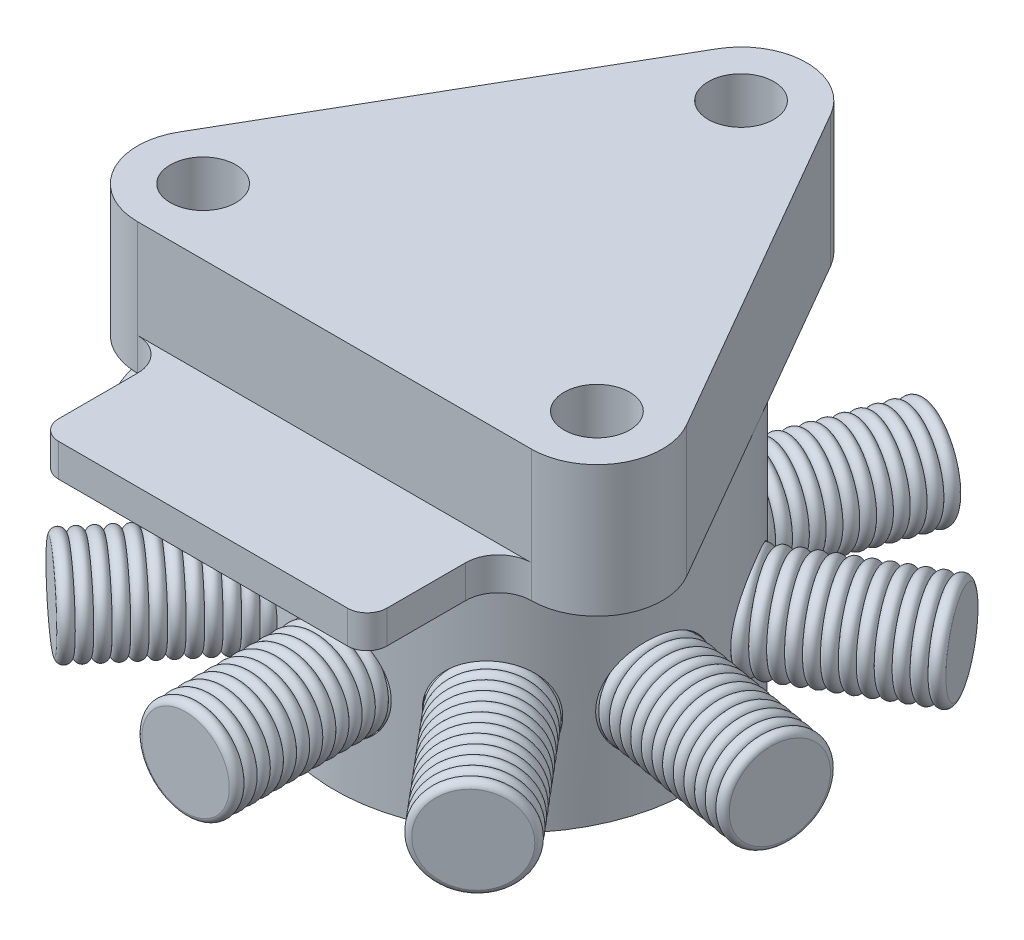
SolidWorks part; units mm, degrees
ref_plane "Plano frontal" through (0, 0, 0) normal (0, 0, 1) x (1, 0, 0)
ref_plane "Plano superior" through (0, 0, 0) normal (0, 1, 0) x (1, 0, 0)
ref_plane "Plano direito" through (0, 0, 0) normal (1, 0, 0) x (0, 0, -1)
sketch "Esboço1" plane through (0, 0, 0) normal (0, 1, 0) x (1, 0, 0)
  line L0 (0.866, 3.9641) -> (3.866, -1.2321)
  line L1 (3, -2.7321) -> (-3, -2.7321)
  line L2 (-3.866, -1.2321) -> (-0.866, 3.9641)
  circle A0 centre (0, 3.4641) radius 0.5
  circle A1 centre (3, -1.7321) radius 0.5
  circle A2 centre (-3, -1.7321) radius 0.5
  arc A3 (0.866, 3.9641) -> (-0.866, 3.9641) centre (0, 3.4641) ccw
  arc A4 (-3.866, -1.2321) -> (-3, -2.7321) centre (-3, -1.7321) ccw
  arc A5 (3, -2.7321) -> (3.866, -1.2321) centre (3, -1.7321) ccw
  circle A6 centre (0, 3.4641) radius 1 construction
  circle A7 centre (-3, -1.7321) radius 1 construction
  circle A8 centre (3, -1.7321) radius 1 construction
  point P10 (0, 0)
  dimension "D2" = 1
  dimension "D1" = 6
  dimension "D4" = 0.5
  dimension "D3" = 3
extrude "Ressalto-extrusão1" add sketch "Esboço1" along normal blind 2
sketch "Esboço2" plane through (0, 0, 0) normal (0, -1, 0) x (1, 0, 0)
  line L0 (0, -55) -> (0, 55) construction
  line L1 (-3, 2.7321) -> (3, 2.7321) construction
  line L2 (-2.5, 3.2321) -> (-2.5, 4.4321)
  line L3 (-2.2, 4.7321) -> (2.2, 4.7321)
  line L4 (2.5, 3.2321) -> (2.5, 4.4321)
  line L5 (-3, 2.7321) -> (3, 2.7321)
  arc A0 (-2.5, 3.2321) -> (-3, 2.7321) centre (-3, 3.2321) cw
  arc A1 (-2.5, 4.4321) -> (-2.2, 4.7321) centre (-2.2, 4.4321) cw
  arc A2 (-3, 2.7321) -> (-3.866, 1.2321) centre (-3, 1.7321) ccw construction
  arc A3 (2.5, 4.4321) -> (2.2, 4.7321) centre (2.2, 4.4321) ccw
  arc A4 (2.5, 3.2321) -> (3, 2.7321) centre (3, 3.2321) ccw
  point P11 (2.4121, 4.6442)
  point P13 (-2.4121, 4.6442)
  point P19 (0, 4.7321)
  dimension "D3" = 0.3
  dimension "D1" = 2
  dimension "D2" = 2.5
extrude "Ressalto-extrusão2" add sketch "Esboço2" against normal blind 0.5
sketch "Esboço3" plane through (0, 0, 0) normal (0, -1, 0) x (-1, 0, 0)
  line L0 (-3.866, -1.2321) -> (-0.866, 3.9641) construction
  circle A0 centre (0, 0) radius 2.7321
extrude "Ressalto-extrusão3" add sketch "Esboço3" along normal blind 4
sketch "Esboço5" plane through (0, 0, 0) normal (0, 0, 1) x (1, 0, 0)
  circle A0 centre (0, -2.5) radius 0.75
  dimension "1,5" = 1.5
  dimension "D2" = 2.5
extrude "Ressalto-extrusão4" add sketch "Esboço5" along normal blind 5
ref_axis "Eixo1" through (0, -2.5, 5) along (0, 0, -1)
ref_plane "Plano2" through (0, -2.5, 0) normal (0, -1, 0) x (-1, 0, 0)
sketch "Esboço7" plane through (0, -2.5, 0) normal (0, -1, 0) x (-1, 0, 0)
  line L0 (-0.75, -5) -> (0.75, -5) construction
  line L1 (-0.75, -2.6271) -> (-0.75, -5) construction
  line L3 (-0.6661, -5) -> (-0.6661, -5.0872)
  line L7 (-0.6661, -5.0872) -> (-0.76, -5.0872)
  line L8 (-0.76, -5.0872) -> (-0.76, -1.9092)
  line L9 (-0.76, -1.9092) -> (-0.6661, -1.9092)
  line L10 (-0.6661, -1.9092) -> (-0.6661, -2)
  arc A0 (-0.6661, -5) -> (-0.6661, -4.8) centre (-0.6485, -4.9) cw
  arc A1 (-0.6661, -4.8) -> (-0.6661, -4.6) centre (-0.6485, -4.7) cw
  arc A2 (-0.6661, -4.6) -> (-0.6661, -4.4) centre (-0.6485, -4.5) cw
  arc A3 (-0.6661, -4.4) -> (-0.6661, -4.2) centre (-0.6485, -4.3) cw
  arc A4 (-0.6661, -4.2) -> (-0.6661, -4) centre (-0.6485, -4.1) cw
  arc A5 (-0.6661, -4) -> (-0.6661, -3.8) centre (-0.6485, -3.9) cw
  arc A6 (-0.6661, -3.8) -> (-0.6661, -3.6) centre (-0.6485, -3.7) cw
  arc A7 (-0.6661, -3.6) -> (-0.6661, -3.4) centre (-0.6485, -3.5) cw
  arc A8 (-0.6661, -3.4) -> (-0.6661, -3.2) centre (-0.6485, -3.3) cw
  arc A9 (-0.6661, -3.2) -> (-0.6661, -3) centre (-0.6485, -3.1) cw
  arc A10 (-0.6661, -3) -> (-0.6661, -2.8) centre (-0.6485, -2.9) cw
  arc A11 (-0.6661, -2.8) -> (-0.6661, -2.6) centre (-0.6485, -2.7) cw
  arc A12 (-0.6661, -2.6) -> (-0.6661, -2.4) centre (-0.6485, -2.5) cw
  arc A13 (-0.6661, -2.4) -> (-0.6661, -2.2) centre (-0.6485, -2.3) cw
  arc A14 (-0.6661, -2.2) -> (-0.6661, -2) centre (-0.6485, -2.1) cw
  point P16 (-0.75, -4.1)
  dimension "D1" = 0.2
  dimension "D2" = 0.0839
  dimension "D4" = 0.01
  dimension "D3" = 15
revolve "Corte-Revolução1" cut sketch "Esboço7" angle 360 about axis through (0, -2.5, 5) along (0, 0, -1)
pattern_circular "PadrãoCircular1" count 9 over 360 about axis through (0, 0, 0) along (0, 1, 0) of "Corte-Revolução1", "Ressalto-extrusão4"
